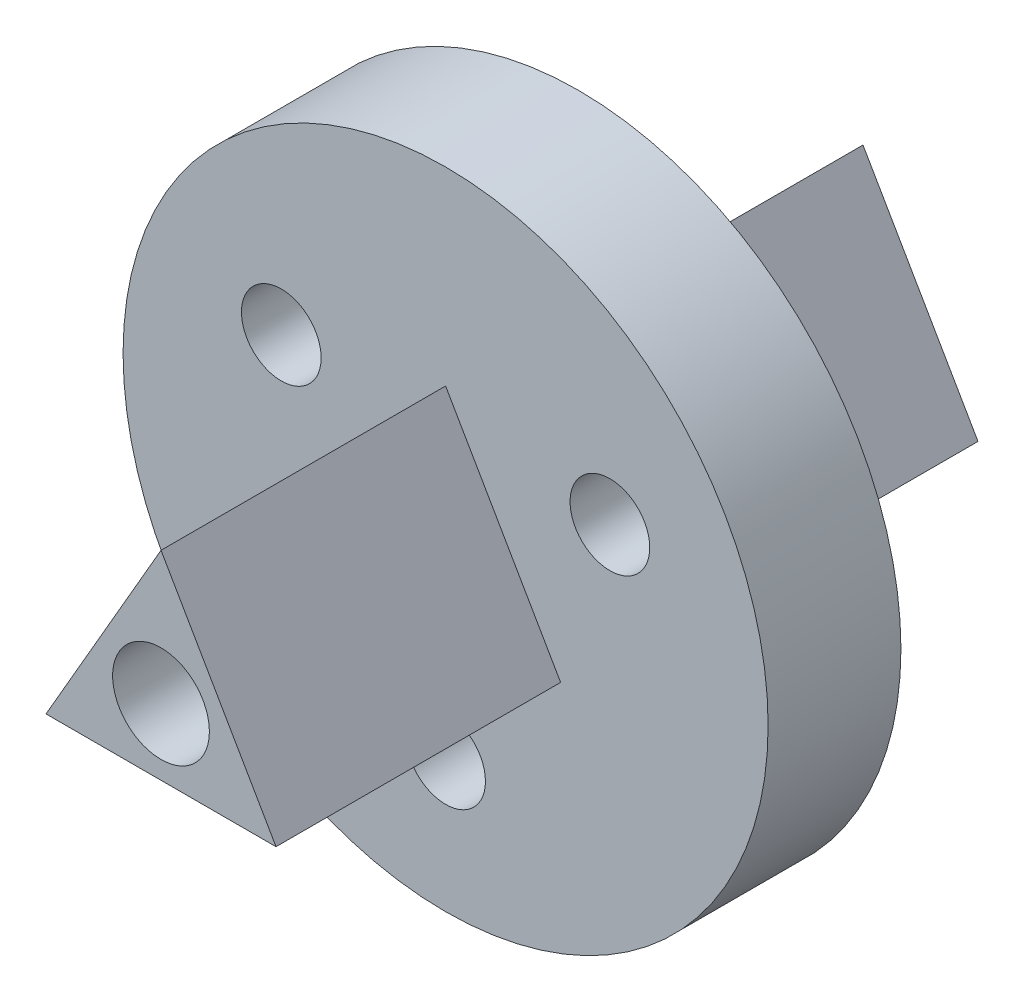
SolidWorks part; units mm, degrees
ref_plane "Front Plane" through (0, 0, 0) normal (0, 0, 1) x (1, 0, 0)
ref_plane "Top Plane" through (0, 0, 0) normal (0, 1, 0) x (1, 0, 0)
ref_plane "Right Plane" through (0, 0, 0) normal (1, 0, 0) x (0, 0, -1)
sketch "Sketch3" plane through (0, 0, 0) normal (0, 0, 1) x (1, 0, 0)
  line L0 (0, 17) -> (0, -17) construction
  line L1 (-14.7224, 8.5) -> (15.5262, -8.964) construction
  line L2 (14.7224, 8.5) -> (-14.7224, -8.5) construction
  circle A0 centre (0, 0) radius 17
  circle A1 centre (8.6603, 5) radius 2.1
  circle A2 centre (0, -10) radius 2.1
  circle A3 centre (-8.6603, 5) radius 2.1
  point P17 (0, 0)
  dimension "D1" = 34
  dimension "D4" = 4.2
  dimension "D2" = 120
  dimension "D3" = 120
  dimension "D5" = 10
  dimension "D6" = 3
extrude "Boss-Extrude1" add sketch "Sketch3" along normal blind 7
sketch "Sketch4" plane through (0, 0, 7) normal (0, 0, 1) x (1, 0, 0)
  line L3 (0, 7) -> (6.0622, -3.5)
  line L4 (-6.0622, -3.5) -> (0, 7)
  line L6 (6.0622, -3.5) -> (-6.0622, -3.5)
  circle A0 centre (0, 0) radius 2.55
  dimension "D1" = 5.1
  dimension "D3" = 7
  dimension "D6" = 7
  dimension "D7" = 7
extrude "Boss-Extrude2" add sketch "Sketch4" along normal blind 15 and the other way blind 22
sketch "Sketch9" plane through (0, 0, 7) normal (0, 0, 1) x (1, 0, 0)
  circle A0 centre (0, 0) radius 2.55
extrude "Cut-Extrude1" cut sketch "Sketch9" against normal through all
